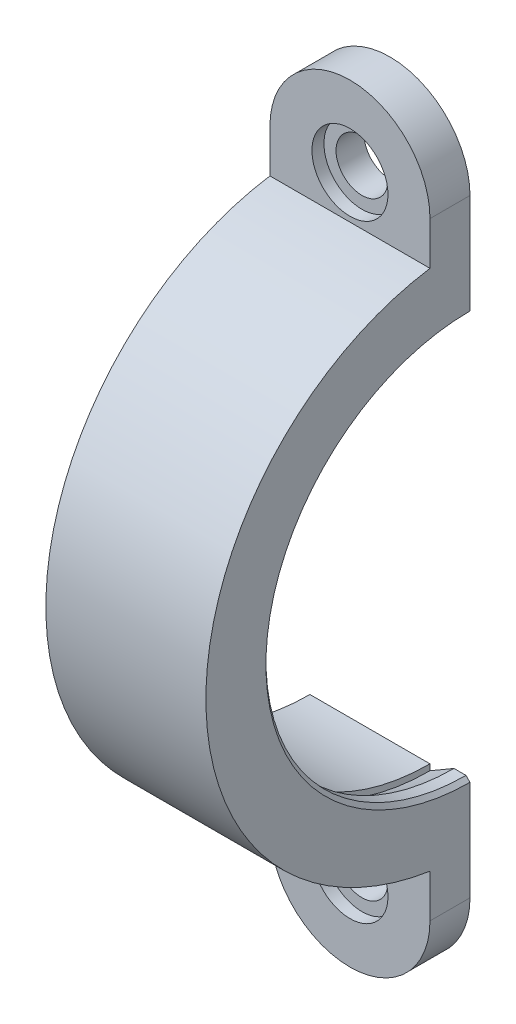
SolidWorks part; units mm, degrees
ref_plane "Front Plane" through (0, 0, 0) normal (0, 0, 1) x (1, 0, 0)
ref_plane "Top Plane" through (0, 0, 0) normal (0, 1, 0) x (1, 0, 0)
ref_plane "Right Plane" through (0, 0, 0) normal (1, 0, 0) x (0, 0, -1)
sketch "Sketch1" plane through (0, 0, 0) normal (0, 0, 1) x (1, 0, 0)
  line L0 (0, 33) -> (20, 33)
  line L1 (18, 25) -> (20, 25)
  line L2 (20, 33) -> (20, 25)
  line L3 (0, 0) -> (50.1034, 0)
  line L4 (0, 33) -> (0, 26)
  line L5 (0, 26) -> (15, 26)
  line L6 (15, 26) -> (15, 26.75)
  line L7 (15, 26.75) -> (18, 25)
  dimension "D1" = 15
  dimension "D2" = 2
  dimension "D3" = 0.75
  dimension "D4" = 3
  dimension "D5" = 1
  dimension "D6" = 7
  dimension "D7" = 26
  dimension "D8" = 0
revolve "Revolve1" add sketch "Sketch1" angle 180 about L3
sketch3d "3DSketch1" plane through (0, 0, 0) normal (0, 0, 1) x (1, 0, 0)
sketch "Sketch9" plane through (0, 0, 0) normal (0, 0, -1) x (-1, 0, 0)
  line L0 (-20, 33) -> (-20, 25) construction
  line L1 (-20, 29) -> (0, 29)
  line L2 (-20, 29) -> (-20, 38)
  line L4 (0, 29) -> (0, 38)
  arc A0 (0, 38) -> (-20, 38) centre (-10, 38) ccw
  dimension "D1" = 5
extrude "Boss-Extrude3" add sketch "Sketch9" against normal blind 5
sketch3d "3DSketch2" plane through (0, 0, 0) normal (0, 0, 1) x (1, 0, 0)
  dimension "D1" = 90
sketch "Sketch11" plane through (0, 0, 0) normal (0, 0, -1) x (-1, 0, 0)
  line L0 (-20, -33) -> (-20, -25) construction
  line L1 (-20, -29) -> (0, -29)
  line L2 (-20, -29) -> (-20, -38)
  line L4 (0, -29) -> (0, -38)
  arc A0 (0, -38) -> (-20, -38) centre (-10, -38) cw
  dimension "D1" = 5
extrude "Boss-Extrude4" add sketch "Sketch11" against normal blind 5
sketch "Sketch17" plane through (0, 0, 0) normal (0, 0, -1) x (-1, 0, 0)
  circle A0 centre (-10, 38) radius 3.2385
  circle A1 centre (-10, -38) radius 3.2385
  dimension "D1" = 6.477
  dimension "D2" = 6.477
extrude "Cut-Extrude1" cut sketch "Sketch17" against normal through all
sketch "Sketch18" plane through (0, 0, 5) normal (0, 0, 1) x (1, 0, 0)
  circle A0 centre (10, -38) radius 4.75
  circle A1 centre (10, 38) radius 4.75
  dimension "D1" = 9.5
  dimension "D2" = 9.5
extrude "Cut-Extrude2" cut sketch "Sketch18" against normal blind 1.5
chamfer "Chamfer1" distance 0.5 angle 45 1 edges at (20, 0, 25)
